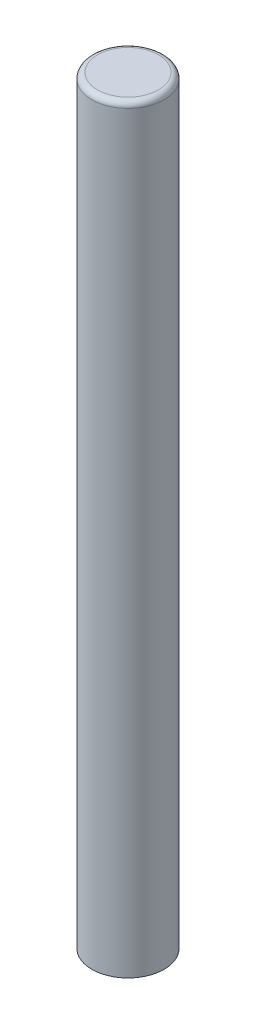
SolidWorks part; units mm, degrees
ref_plane "Front Plane" through (0, 0, 0) normal (0, 0, 1) x (1, 0, 0)
ref_plane "Top Plane" through (0, 0, 0) normal (0, 1, 0) x (1, 0, 0)
ref_plane "Right Plane" through (0, 0, 0) normal (1, 0, 0) x (0, 0, -1)
sketch "Sketch1" plane through (0, 0, 0) normal (0, 1, 0) x (1, 0, 0)
  circle A0 centre (0, 0) radius 9.525
  dimension "D1" = 19.05
extrude "Boss-Extrude1" add sketch "Sketch1" along normal blind 200
fillet "Fillet1" radius 1.5 1 edges at (0, 200, 9.525)
